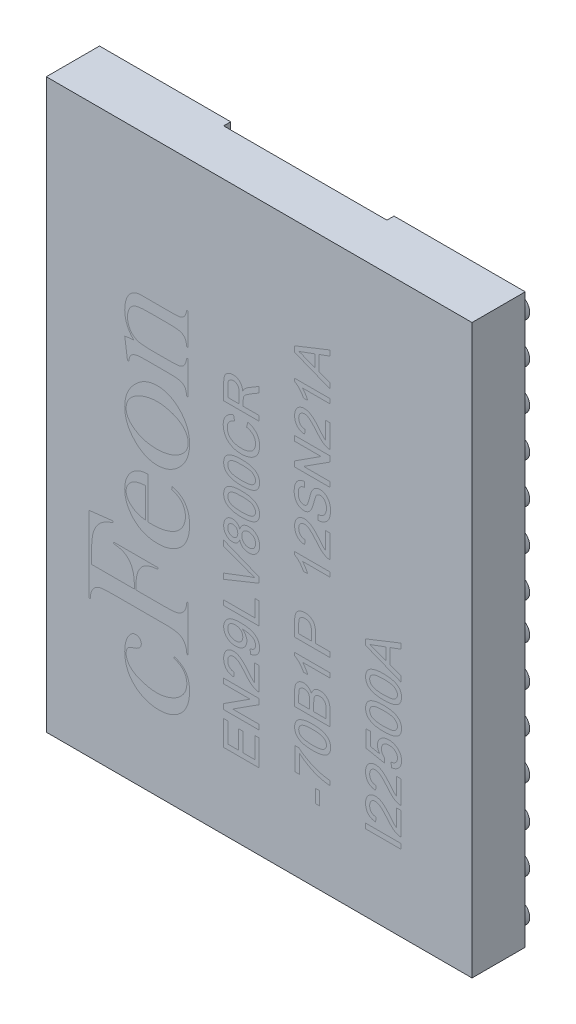
SolidWorks part; units mm, degrees
ref_plane "Спереди" through (0, 0, 0) normal (0, 0, 1) x (1, 0, 0)
ref_plane "Сверху" through (0, 0, 0) normal (0, 1, 0) x (1, 0, 0)
ref_plane "Справа" through (0, 0, 0) normal (1, 0, 0) x (0, 0, -1)
sketch "Эскиз1" plane through (0, 0, 0) normal (0, 0, 1) x (1, 0, 0)
  line L1 (3, 4) -> (-3, 4)
  line L2 (3, 4) -> (3, -4)
  line L3 (3, -4) -> (-3, -4)
  line L4 (-3, 4) -> (-3, -4)
  line L5 (3, 4) -> (-3, -4) construction
  line L6 (3, -4) -> (-3, 4) construction
  point P0 (0, 0)
  dimension "D1" = 6
  dimension "D2" = 8
extrude "Бобышка-Вытянуть1" add sketch "Эскиз1" along normal blind 0.75
sketch "Эскиз2" plane through (0, 0, 0) normal (0, 0, -1) x (-1, 0, 0)
  line L0 (0, -4) -> (0, 4) construction
  line L1 (3, -4) -> (-3, -4) construction
  line L2 (-3, 4) -> (3, 4) construction
  line L3 (3, 0) -> (-3, 0) construction
  line L4 (3, 4) -> (3, -4) construction
  line L5 (-3, -4) -> (-3, 4) construction
  line L6 (3, 4) -> (2.809, 4) construction
  line L7 (2.809, 4) -> (2.809, 3.68) construction
  line L8 (2.809, -4) -> (2.809, -3.68) construction
  line L9 (3, -4) -> (2.809, -4) construction
  line L10 (-3, -4) -> (-2.809, -4) construction
  line L11 (-2.809, -3.11) -> (-2.809, -3.705) construction
  line L12 (-2.809, 4) -> (-2.809, 3.68) construction
  line L13 (-3, 4) -> (-2.809, 4) construction
  circle A0 centre (2.809, 3.68) radius 0.154
  circle A1 centre (2.809, 3.11) radius 0.154
  circle A2 centre (2.809, 2.54) radius 0.154
  circle A3 centre (2.809, 1.97) radius 0.154
  circle A4 centre (2.809, 1.4) radius 0.154
  circle A5 centre (2.809, 0.83) radius 0.154
  circle A6 centre (2.809, 0.26) radius 0.154
  circle A14 centre (2.359, 3.11) radius 0.154
  circle A15 centre (2.359, 2.54) radius 0.154
  circle A16 centre (2.359, 1.97) radius 0.154
  circle A17 centre (2.359, 1.4) radius 0.154
  circle A18 centre (2.359, 0.83) radius 0.154
  circle A19 centre (2.359, 0.26) radius 0.154
  circle A27 centre (1.909, 3.11) radius 0.154
  circle A28 centre (1.909, 2.54) radius 0.154
  circle A29 centre (1.909, 1.97) radius 0.154
  circle A30 centre (1.909, 1.4) radius 0.154
  circle A31 centre (1.909, 0.83) radius 0.154
  circle A32 centre (1.909, 0.26) radius 0.154
  circle A40 centre (1.459, 3.11) radius 0.154
  circle A41 centre (1.459, 2.54) radius 0.154
  circle A42 centre (1.459, 1.97) radius 0.154
  circle A43 centre (1.459, 1.4) radius 0.154
  circle A44 centre (1.459, 0.83) radius 0.154
  circle A45 centre (1.459, 0.26) radius 0.154
  circle A53 centre (2.359, 3.68) radius 0.154
  circle A54 centre (1.909, 3.68) radius 0.154
  circle A55 centre (1.459, 3.68) radius 0.154
  circle A112 centre (2.809, -0.31) radius 0.154 [skipped]
  circle A113 centre (2.809, -0.88) radius 0.154 [skipped]
  circle A114 centre (2.809, -1.45) radius 0.154 [skipped]
  circle A115 centre (2.809, -2.02) radius 0.154 [skipped]
  circle A116 centre (2.809, -2.59) radius 0.154 [skipped]
  circle A117 centre (2.809, -3.16) radius 0.154 [skipped]
  circle A118 centre (2.809, -3.73) radius 0.154 [skipped]
  circle A119 centre (2.359, -0.31) radius 0.154 [skipped]
  circle A120 centre (2.359, -0.88) radius 0.154 [skipped]
  circle A121 centre (2.359, -1.45) radius 0.154 [skipped]
  circle A122 centre (2.359, -2.02) radius 0.154 [skipped]
  circle A123 centre (2.359, -2.59) radius 0.154 [skipped]
  circle A124 centre (2.359, -3.16) radius 0.154 [skipped]
  circle A125 centre (2.359, -3.73) radius 0.154 [skipped]
  circle A126 centre (1.909, -0.31) radius 0.154 [skipped]
  circle A127 centre (1.909, -0.88) radius 0.154 [skipped]
  circle A128 centre (1.909, -1.45) radius 0.154 [skipped]
  circle A129 centre (1.909, -2.02) radius 0.154 [skipped]
  circle A130 centre (1.909, -2.59) radius 0.154 [skipped]
  circle A131 centre (1.909, -3.16) radius 0.154 [skipped]
  circle A132 centre (1.909, -3.73) radius 0.154 [skipped]
  circle A133 centre (1.459, -0.31) radius 0.154 [skipped]
  circle A134 centre (1.459, -0.88) radius 0.154 [skipped]
  circle A135 centre (1.459, -1.45) radius 0.154 [skipped]
  circle A136 centre (1.459, -2.02) radius 0.154 [skipped]
  circle A137 centre (1.459, -2.59) radius 0.154 [skipped]
  circle A138 centre (1.459, -3.16) radius 0.154 [skipped]
  circle A139 centre (1.459, -3.73) radius 0.154 [skipped]
  circle A140 centre (1.459, -3.68) radius 0.154
  circle A141 centre (1.909, -3.68) radius 0.154
  circle A142 centre (2.359, -3.68) radius 0.154
  circle A143 centre (1.459, -0.26) radius 0.154
  circle A144 centre (1.459, -0.83) radius 0.154
  circle A145 centre (1.459, -1.4) radius 0.154
  circle A146 centre (1.459, -1.97) radius 0.154
  circle A147 centre (1.459, -2.54) radius 0.154
  circle A148 centre (1.459, -3.11) radius 0.154
  circle A149 centre (1.909, -0.26) radius 0.154
  circle A150 centre (1.909, -0.83) radius 0.154
  circle A151 centre (1.909, -1.4) radius 0.154
  circle A152 centre (1.909, -1.97) radius 0.154
  circle A153 centre (1.909, -2.54) radius 0.154
  circle A154 centre (1.909, -3.11) radius 0.154
  circle A155 centre (2.359, -0.26) radius 0.154
  circle A156 centre (2.359, -0.83) radius 0.154
  circle A157 centre (2.359, -1.4) radius 0.154
  circle A158 centre (2.359, -1.97) radius 0.154
  circle A159 centre (2.359, -2.54) radius 0.154
  circle A160 centre (2.359, -3.11) radius 0.154
  circle A161 centre (2.809, -0.26) radius 0.154
  circle A162 centre (2.809, -0.83) radius 0.154
  circle A163 centre (2.809, -1.4) radius 0.154
  circle A164 centre (2.809, -1.97) radius 0.154
  circle A165 centre (2.809, -2.54) radius 0.154
  circle A166 centre (2.809, -3.11) radius 0.154
  circle A169 centre (-2.809, -3.11) radius 0.154
  circle A170 centre (-2.809, -2.54) radius 0.154
  circle A171 centre (-2.809, -1.97) radius 0.154
  circle A172 centre (-2.809, -1.4) radius 0.154
  circle A173 centre (-2.809, -0.83) radius 0.154
  circle A174 centre (-2.809, -0.26) radius 0.154
  circle A175 centre (-2.359, -3.11) radius 0.154
  circle A176 centre (-2.359, -2.54) radius 0.154
  circle A177 centre (-2.359, -1.97) radius 0.154
  circle A178 centre (-2.359, -1.4) radius 0.154
  circle A179 centre (-2.359, -0.83) radius 0.154
  circle A180 centre (-2.359, -0.26) radius 0.154
  circle A181 centre (-1.909, -3.11) radius 0.154
  circle A182 centre (-1.909, -2.54) radius 0.154
  circle A183 centre (-1.909, -1.97) radius 0.154
  circle A184 centre (-1.909, -1.4) radius 0.154
  circle A185 centre (-1.909, -0.83) radius 0.154
  circle A186 centre (-1.909, -0.26) radius 0.154
  circle A187 centre (-1.459, -3.11) radius 0.154
  circle A188 centre (-1.459, -2.54) radius 0.154
  circle A189 centre (-1.459, -1.97) radius 0.154
  circle A190 centre (-1.459, -1.4) radius 0.154
  circle A191 centre (-1.459, -0.83) radius 0.154
  circle A192 centre (-1.459, -0.26) radius 0.154
  circle A193 centre (-2.359, -3.68) radius 0.154
  circle A194 centre (-1.909, -3.68) radius 0.154
  circle A195 centre (-1.459, -3.68) radius 0.154
  circle A196 centre (-1.459, 3.68) radius 0.154
  circle A197 centre (-1.909, 3.68) radius 0.154
  circle A198 centre (-2.359, 3.68) radius 0.154
  circle A199 centre (-1.459, 0.26) radius 0.154
  circle A200 centre (-1.459, 0.83) radius 0.154
  circle A201 centre (-1.459, 1.4) radius 0.154
  circle A202 centre (-1.459, 1.97) radius 0.154
  circle A203 centre (-1.459, 2.54) radius 0.154
  circle A204 centre (-1.459, 3.11) radius 0.154
  circle A205 centre (-1.909, 0.26) radius 0.154
  circle A206 centre (-1.909, 0.83) radius 0.154
  circle A207 centre (-1.909, 1.4) radius 0.154
  circle A208 centre (-1.909, 1.97) radius 0.154
  circle A209 centre (-1.909, 2.54) radius 0.154
  circle A210 centre (-1.909, 3.11) radius 0.154
  circle A211 centre (-2.359, 0.26) radius 0.154
  circle A212 centre (-2.359, 0.83) radius 0.154
  circle A213 centre (-2.359, 1.4) radius 0.154
  circle A214 centre (-2.359, 1.97) radius 0.154
  circle A215 centre (-2.359, 2.54) radius 0.154
  circle A216 centre (-2.359, 3.11) radius 0.154
  circle A217 centre (-2.809, 0.26) radius 0.154
  circle A218 centre (-2.809, 0.83) radius 0.154
  circle A219 centre (-2.809, 1.4) radius 0.154
  circle A220 centre (-2.809, 1.97) radius 0.154
  circle A221 centre (-2.809, 2.54) radius 0.154
  circle A222 centre (-2.809, 3.11) radius 0.154
  circle A223 centre (-2.809, 3.68) radius 0.154
  circle A224 centre (-2.809, -3.705) radius 0.154
  dimension "D1" = 14
  dimension "D3" = 0.308
  dimension "D4" = 0.32
  dimension "D2" = 4
extrude "Бобышка-Вытянуть2" add sketch "Эскиз2" along normal blind 0.1
sketch "Эскиз5" plane through (0, 0, 0) normal (0, 0, -1) x (-1, 0, 0)
  line L0 (-3, 4) -> (3, 4) construction
  line L1 (-1.1505, 3.215) -> (1.1505, 3.215)
  line L2 (-1.1505, 3.215) -> (-1.1505, 4)
  line L3 (-1.1505, 4) -> (1.1505, 4)
  line L4 (1.1505, 3.215) -> (1.1505, 4)
  line L5 (3, -4) -> (-3, -4) construction
  line L6 (-1.1505, -3.215) -> (1.1505, -3.215)
  line L7 (-1.1505, -3.215) -> (-1.1505, -4)
  line L8 (-1.1505, -4) -> (1.1505, -4)
  line L9 (1.1505, -3.215) -> (1.1505, -4)
  point P15 (0, -4)
  point P17 (0, 3.215)
extrude "Вырез-Вытянуть3" cut sketch "Эскиз5" against normal blind 0.1
sketch "Эскиз3" plane through (0, 0, 0) normal (0, 0, -1) x (-1, 0, 0)
  line L0 (-1.1505, 4) -> (-1.1505, 3.215) construction
  line L9 (1.1505, 3.215) -> (-1.1505, 3.215)
  line L10 (1.1505, 3.215) -> (1.1505, -3.215)
  line L11 (1.1505, -3.215) -> (-1.1505, -3.215)
  line L12 (-1.1505, 3.215) -> (-1.1505, -3.215)
  point P0 (0, 3.215)
extrude "Вырез-Вытянуть2" cut sketch "Эскиз3" against normal blind 0.07
sketch "Sketch1" [suppressed] plane through (0, 0, 2) normal (0, 0, 1) x (1, 0, 0)
  line L0 (0, 0) -> (0, -0.5) construction
  line L1 (-3.4888, -0.5) -> (3.4888, -0.5) construction
  line L2 (-3.4888, -1.75) -> (3.4888, -1.75) construction
  line L3 (-3.4888, -3) -> (3.4888, -3) construction
  line L4 (-1.4092, 0.6238) -> (0.357, 0.6238)
  line L5 (0.357, 0.6238) -> (1.0627, 1.3228)
  line L6 (1.0962, 1.3038) -> (0.9219, 0.6064)
  line L7 (1.0328, 0.6064) -> (1.2808, 0.6064)
  line L8 (1.3008, 0.6264) -> (1.3008, 1.6963)
  line L9 (1.2708, 1.7263) -> (0.5438, 1.7263)
  line L10 (0.9219, 0.6064) -> (1.0328, 0.6064)
  line L11 (-1.4292, 0.6438) -> (-1.4292, 0.7212)
  line L12 (-1.4092, 0.7412) -> (0.3108, 0.7412)
  line L13 (0.3108, 0.7412) -> (0.9772, 1.4076)
  line L14 (0.9681, 1.4245) -> (0.2822, 1.2827)
  line L15 (-1.4292, 1.3008) -> (-1.4292, 1.4549)
  line L16 (-0.2926, 2.4499) -> (0.7741, 2.4499) construction
  line L17 (0.2468, 1.4313) -> (0.909, 1.5375)
  line L18 (0.9074, 1.5574) -> (0.536, 1.5574)
  line L19 (-1.4292, 2.4499) -> (-1.4292, 2.8482)
  line L20 (-1.3992, 2.8782) -> (-0.9028, 2.8782)
  line L21 (-3.2533, 3.2573) -> (-2.6533, 3.2573)
  line L22 (-3.2533, 3.2573) -> (-3.2533, 2.6573)
  line L23 (-3.2533, 2.6573) -> (-2.6533, 2.6573)
  line L24 (-2.6533, 3.2573) -> (-2.6533, 2.6573)
  line L25 (-3.2533, 3.2573) -> (-2.6533, 2.6573) construction
  line L26 (-3.2533, 2.6573) -> (-2.6533, 3.2573) construction
  arc A0 (0.2822, 1.2827) -> (-1.4114, 1.2809) centre (-0.5729, 9.0729) cw
  arc A1 (-1.4064, 1.4747) -> (0.2468, 1.4313) centre (-0.3872, 8.7808) ccw
  arc A2 (-1.4119, 2.412) -> (0.536, 1.5574) centre (0.947, 5.1414) ccw
  arc A3 (0.5438, 1.7263) -> (-0.8559, 2.8456) centre (0.7741, 3.449) cw
  arc A4 (1.2808, 0.6064) -> (1.3008, 0.6264) centre (1.2808, 0.6264) ccw
  arc A5 (1.0627, 1.3228) -> (1.0962, 1.3038) centre (1.0768, 1.3086) cw
  arc A6 (-1.4292, 1.3008) -> (-1.4114, 1.2809) centre (-1.4092, 1.3008) ccw
  arc A7 (-1.4292, 1.4549) -> (-1.4064, 1.4747) centre (-1.4092, 1.4549) cw
  arc A8 (-1.4292, 0.7212) -> (-1.4092, 0.7412) centre (-1.4092, 0.7212) cw
  arc A9 (-1.4092, 0.6238) -> (-1.4292, 0.6438) centre (-1.4092, 0.6438) cw
  arc A10 (0.9772, 1.4076) -> (0.9681, 1.4245) centre (0.9701, 1.4147) ccw
  arc A11 (0.909, 1.5375) -> (0.9074, 1.5574) centre (0.9074, 1.5474) ccw
  arc A12 (1.3008, 1.6963) -> (1.2708, 1.7263) centre (1.2708, 1.6963) ccw
  arc A13 (-1.4292, 2.4499) -> (-1.4119, 2.412) centre (-1.3792, 2.4499) ccw
  arc A14 (-0.9028, 2.8782) -> (-0.8559, 2.8456) centre (-0.9028, 2.8282) cw
  arc A15 (-1.4292, 2.8482) -> (-1.3992, 2.8782) centre (-1.3992, 2.8482) cw
  text T0 "BC417" font "Arial" height 0.75
  text T1 "143BG0" font "Arial" height 0.75
  text T2 "K210DJ" font "Arial" height 0.75
  text T3 "csr" font "Arial" height 0.75
  point P6 (0, -0.5)
  point P10 (0, -1.75)
  point P12 (0, -3)
  point P49 (-1.4292, 1.4779)
  point P52 (-1.4292, 0.7412)
  point P72 (-2.9533, 2.9573)
  dimension "D4" = 0.02
  dimension "D5" = 0.01
  dimension "D6" = 0.03
  dimension "D7" = 0.05
  dimension "D8" = 0.03
  dimension "D1" = 0.5
  dimension "D2" = 1.25
  dimension "D3" = 1.25
  dimension "D9" = 0.6
sketch "Sketch2" plane through (0, 0, 0.75) normal (0, 0, 1) x (1, 0, 0)
  line L0 (-1, -2.9936) -> (-1, 3.238) construction
  line L1 (0, -2.9936) -> (0, 3.238) construction
  line L2 (1, -2.9936) -> (1, 3.238) construction
  line L3 (2, -2.9936) -> (2, 3.238) construction
  text T0 "cFeon" font "Baskerville Old Face" height 1.4
  text T1 "EN29LV800CR" font "Arial" height 0.5
  text T2 "-70B1P  12SN21A" font "Arial" height 0.5
  text T3 "I22500A" font "Arial" height 0.5
  point P3 (-1, 0.1222)
  dimension "D1" = 1
  dimension "D2" = 1
  dimension "D3" = 1
  dimension "D4" = 1
split line "Split Line1"
